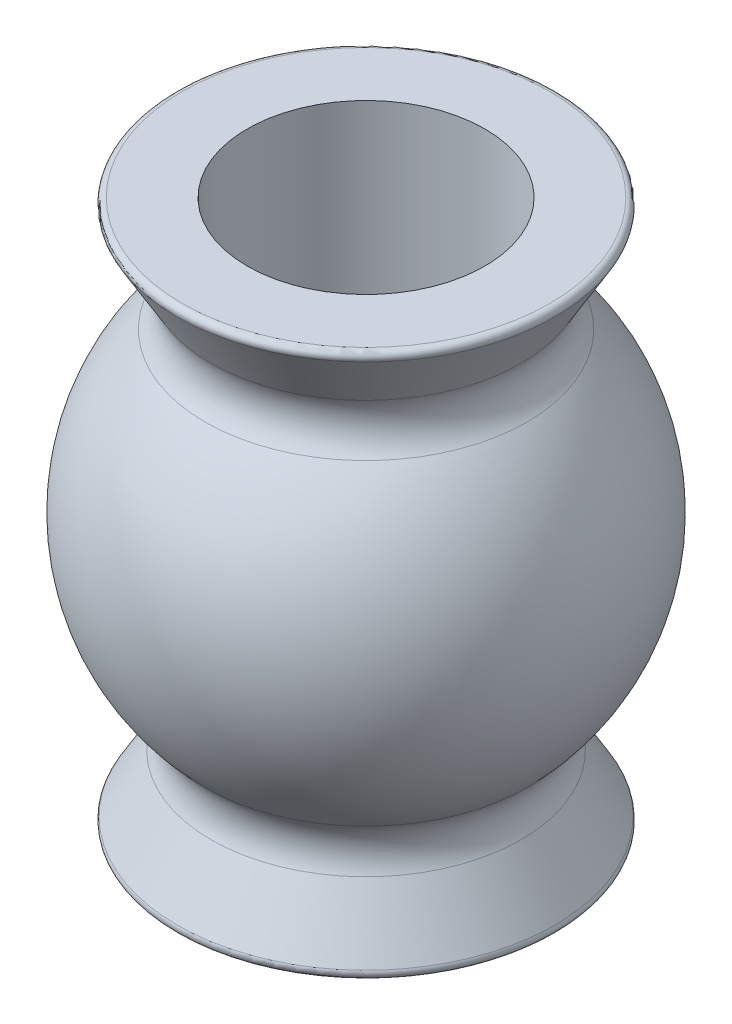
SolidWorks part; units mm, degrees
ref_plane "Front Plane" through (0, 0, 0) normal (0, 0, 1) x (1, 0, 0)
ref_plane "Top Plane" through (0, 0, 0) normal (0, 1, 0) x (1, 0, 0)
ref_plane "Right Plane" through (0, 0, 0) normal (1, 0, 0) x (0, 0, -1)
sketch "Sketch1" plane through (0, 0, 0) normal (0, 0, 1) x (1, 0, 0)
  line L0 (1.524, 0) -> (1.524, 6.985)
  line L1 (1.524, 6.985) -> (2.4892, 6.985)
  line L2 (2.4892, 6.985) -> (1.7773, 5.7785)
  line L3 (1.7773, 1.2065) -> (2.4892, 0)
  line L4 (2.4892, 0) -> (1.524, 0)
  line L5 (0, 0) -> (0, 7.7819) construction
  arc A0 (1.7773, 5.7785) -> (1.7773, 1.2065) centre (0, 3.4925) cw
  point P10 (1.524, 3.4925)
  dimension "D3" = 2.8956
  dimension "D1" = 3.048
  dimension "D2" = 6.985
  dimension "D4" = 4.9784
  dimension "D5" = 4.572
revolve "Revolve1" add sketch "Sketch1" angle 360 about L5
fillet "Fillet1" radius 0.508 2 edges at (0, 1.2065, -1.7773) (0, 5.7785, -1.7773)
fillet "Fillet2" radius 0.0762 2 edges at (0, 0, -2.4892) (0, 6.985, -2.4892)
